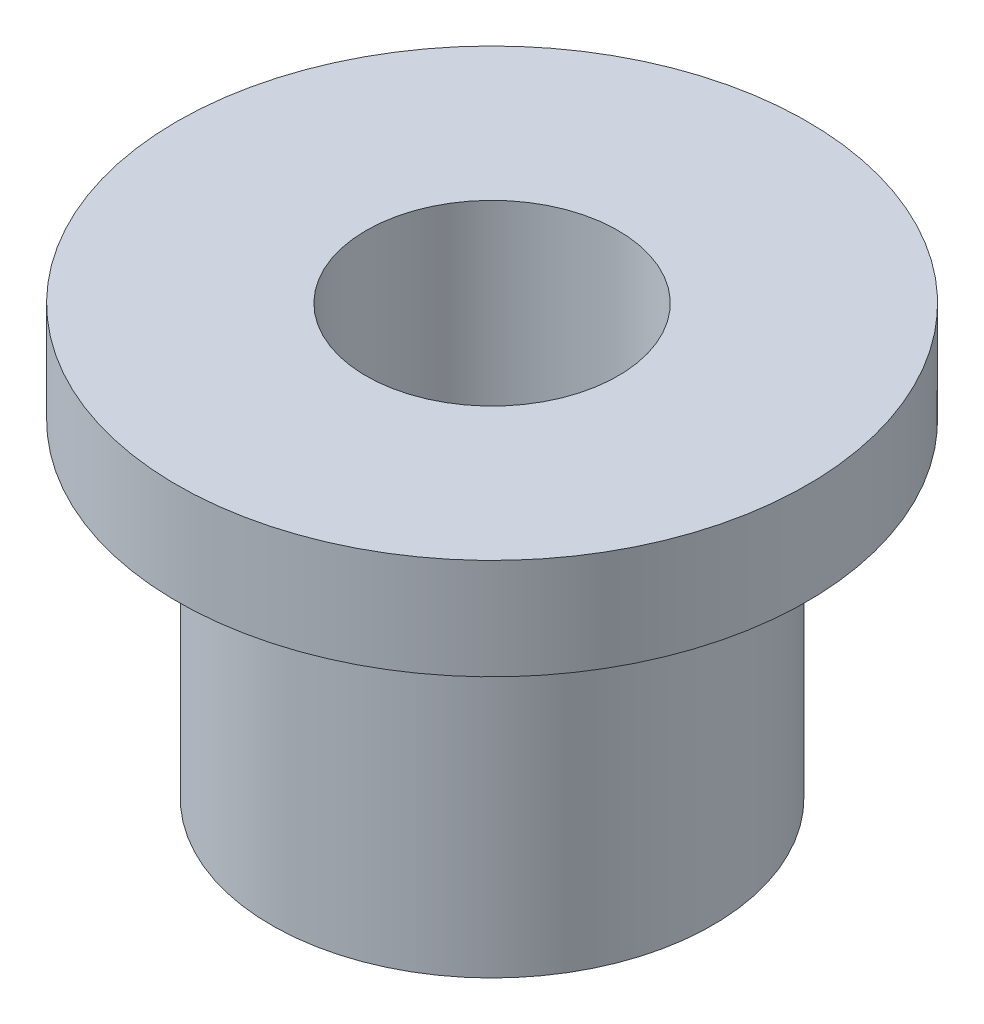
SolidWorks part; units mm, degrees
material "Aluminum Bronze"
ref_plane "Front Plane" through (0, 0, 0) normal (0, 0, 1) x (1, 0, 0)
ref_plane "Top Plane" through (0, 0, 0) normal (0, 1, 0) x (1, 0, 0)
ref_plane "Right Plane" through (0, 0, 0) normal (1, 0, 0) x (0, 0, -1)
sketch "Sketch1" plane through (0, 0, 0) normal (0, 0, 1) x (1, 0, 0)
  line L0 (0, 34.031) -> (0, -34.031) construction
  line L1 (0, 0) -> (17.5, 0)
  line L2 (17.5, 0) -> (17.5, 26)
  line L3 (17.5, 26) -> (25, 26)
  line L4 (25, 26) -> (25, 34)
  line L5 (25, 34) -> (0, 34)
  line L6 (0, 0) -> (0, 34)
  point P4 (0, 0)
  point P7 (0, 34.031)
  point P12 (25, 30)
  dimension "D1" = 35
  dimension "D2" = 26
  dimension "D3" = 8
  dimension "D4" = 50
revolve "Revolve1" add sketch "Sketch1" angle 360 about L0
sketch "Sketch2" plane through (0, 34, 0) normal (0, 1, 0) x (1, 0, 0)
  circle A0 centre (0, 0) radius 10
  dimension "D1" = 20
extrude "Cut-Extrude1" cut sketch "Sketch2" against normal up to next
